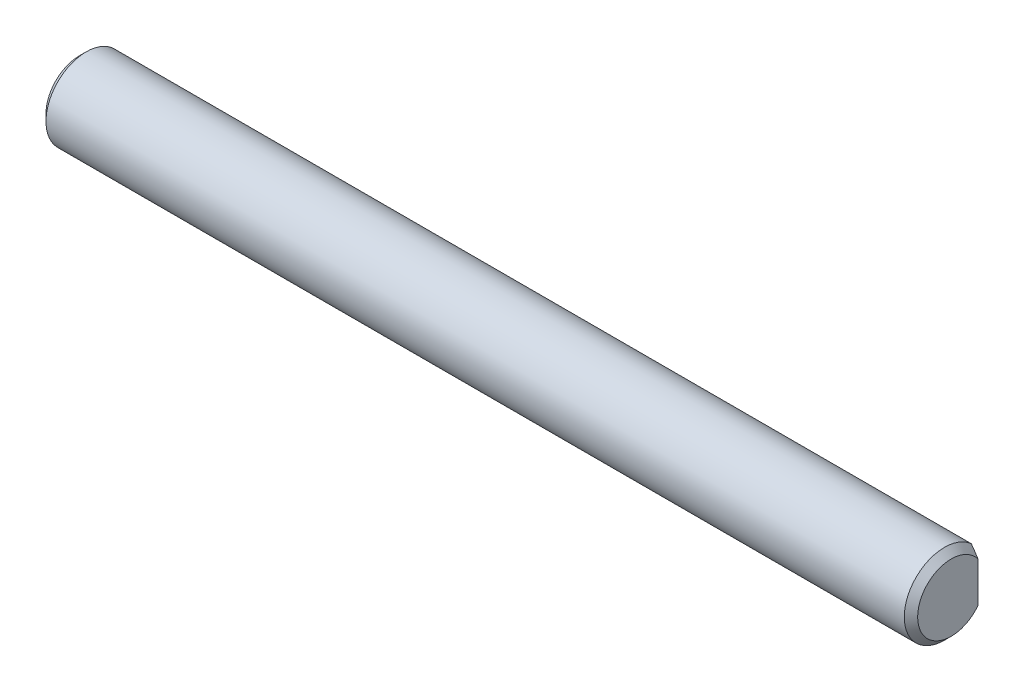
SolidWorks part; units mm, degrees
ref_plane "Front Plane" through (0, 0, 0) normal (0, 0, 1) x (1, 0, 0)
ref_plane "Top Plane" through (0, 0, 0) normal (0, 1, 0) x (1, 0, 0)
ref_plane "Right Plane" through (0, 0, 0) normal (1, 0, 0) x (0, 0, -1)
sketch "Sketch1" plane through (0, 0, 0) normal (1, 0, 0) x (0, 0, -1)
  circle A0 centre (0, 0) radius 3
extrude "Boss-Extrude1" add sketch "Sketch1" along normal blind 65
chamfer "Chamfer1" distance 0.5 angle 45 2 edges at (65, 0, -3) (0, 0, -3)
sketch "Sketch2" plane through (65, 0, 0) normal (1, 0, 0) x (0, 0, -1)
  line L0 (0, 2.0659) -> (0, -5.88) construction
  line L4 (2, 3.2006) -> (2, -3.2006)
  arc A0 (2, 3.2006) -> (2, -3.2006) centre (2.686, 0) cw
  dimension "D1" = 2
extrude "Cut-Extrude1" cut sketch "Sketch2" against normal blind 8
